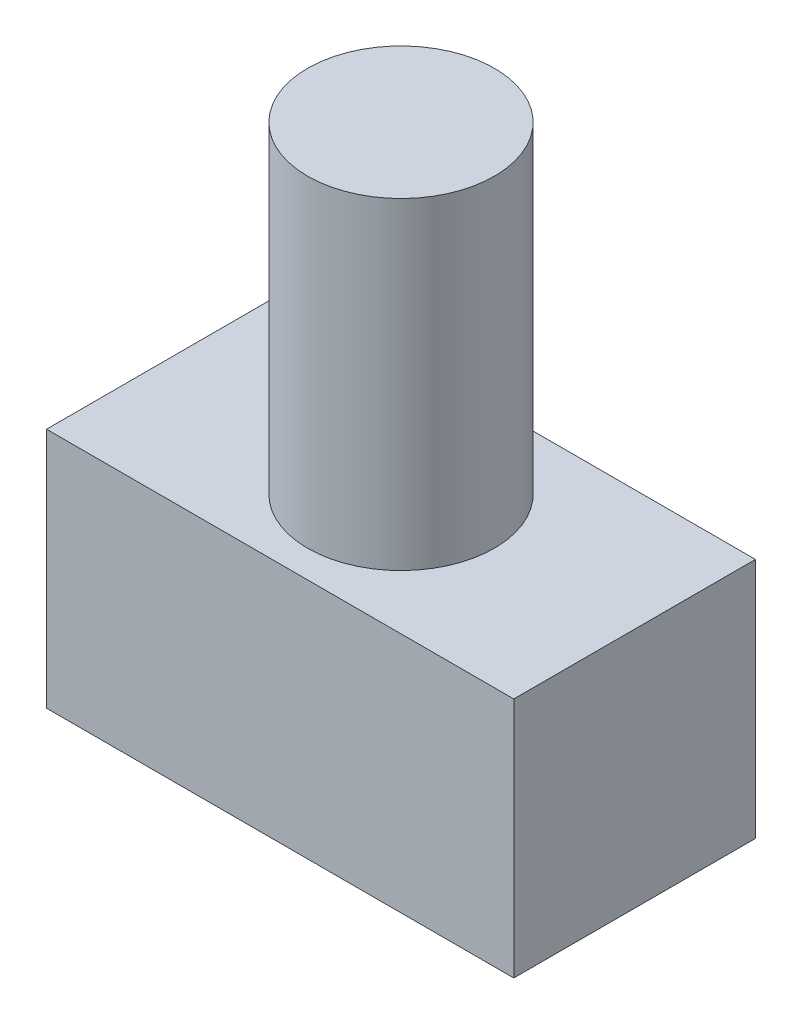
SolidWorks part; units mm, degrees
ref_plane "Front Plane" through (0, 0, 0) normal (0, 0, 1) x (1, 0, 0)
ref_plane "Top Plane" through (0, 0, 0) normal (0, 1, 0) x (1, 0, 0)
ref_plane "Right Plane" through (0, 0, 0) normal (1, 0, 0) x (0, 0, -1)
sketch "Sketch1" plane through (0, 0, 0) normal (0, 0, 1) x (1, 0, 0)
  line L1 (-14.5, 7.5) -> (14.5, 7.5)
  line L2 (-14.5, 7.5) -> (-14.5, -7.5)
  line L3 (-14.5, -7.5) -> (14.5, -7.5)
  line L4 (14.5, 7.5) -> (14.5, -7.5)
  line L5 (-14.5, 7.5) -> (14.5, -7.5) construction
  line L6 (-14.5, -7.5) -> (14.5, 7.5) construction
  point P0 (0, 0)
  dimension "D1" = 29
  dimension "D2" = 15
extrude "Boss-Extrude1" add sketch "Sketch1" along normal blind 15
sketch "Sketch2" plane through (0, 7.5, 0) normal (0, 1, 0) x (1, 0, 0)
  line L0 (-14.5, -7.5) -> (14.5, -7.5) construction
  line L1 (-14.5, -15) -> (-14.5, 0) construction
  line L2 (14.5, -15) -> (14.5, 0) construction
  line L3 (0, -15) -> (0, 0) construction
  line L4 (14.5, -15) -> (-14.5, -15) construction
  circle A0 centre (0, -7.5) radius 5.8
  dimension "D1" = 11.6
extrude "Boss-Extrude2" add sketch "Sketch2" along normal blind 20
sketch "Sketch3" plane through (0, 0, 0) normal (0, 0, -1) x (-1, 0, 0)
  line L0 (0, 7.5) -> (0, -7.5) construction
  line L1 (-14.5, 7.5) -> (14.5, 7.5) construction
  line L2 (14.5, -7.5) -> (-14.5, -7.5) construction
  line L3 (-14.5, 0) -> (14.5, 0) construction
  line L4 (-14.5, -7.5) -> (-14.5, 7.5) construction
  line L5 (14.5, 7.5) -> (14.5, -7.5) construction
  circle A0 centre (0, 0) radius 2.5
  dimension "D1" = 5
extrude "Cut-Extrude1" cut sketch "Sketch3" against normal blind 8 contours A0
